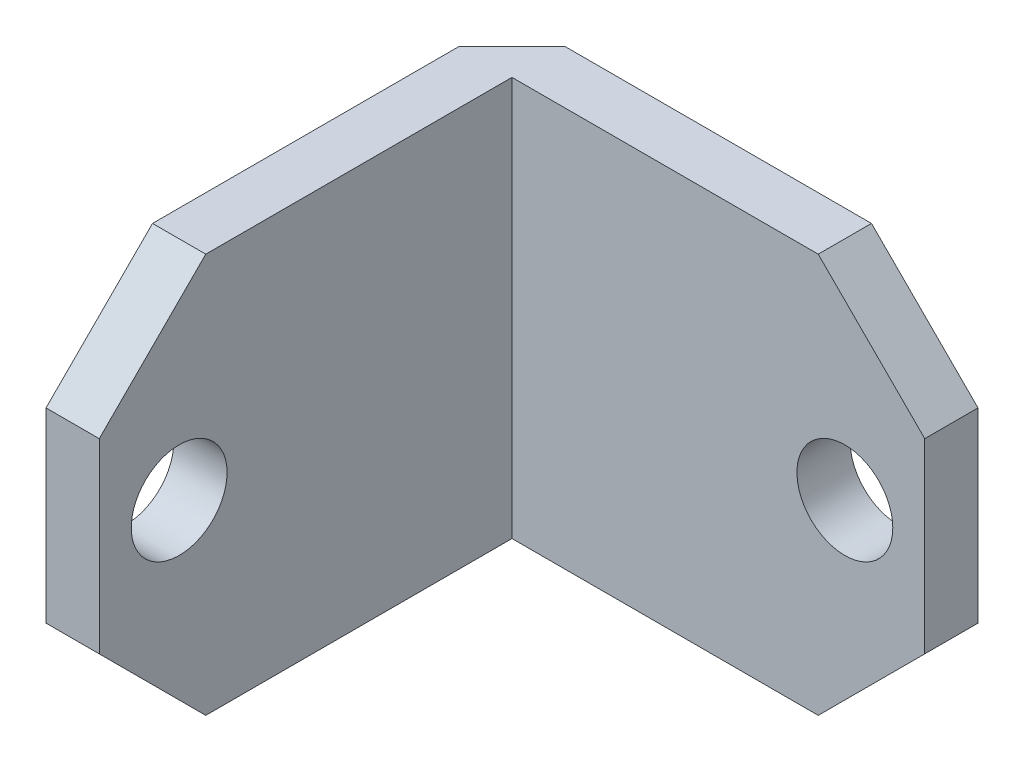
SolidWorks part; units mm, degrees
ref_plane "Front Plane" through (0, 0, 0) normal (0, 0, 1) x (1, 0, 0)
ref_plane "Top Plane" through (0, 0, 0) normal (0, 1, 0) x (1, 0, 0)
ref_plane "Right Plane" through (0, 0, 0) normal (1, 0, 0) x (0, 0, -1)
sketch "Sketch1" plane through (0, 0, 0) normal (0, 1, 0) x (1, 0, 0)
  line L1 (0, 0) -> (2.54, 0)
  line L2 (0, 0) -> (0, 22.225)
  line L4 (2.54, 0) -> (2.54, 19.685)
  line L5 (0, 22.225) -> (22.225, 22.225)
  line L6 (0, 22.225) -> (0, 14.8757)
  line L7 (2.54, 19.685) -> (22.225, 19.685)
  line L8 (22.225, 22.225) -> (22.225, 19.685)
  dimension "D1" = 19.685
  dimension "D3" = 2.54
  dimension "D4" = 2.54
extrude "Boss-Extrude1" add sketch "Sketch1" along normal blind 19.05 contours L8 L5 L2 L1 L4 L7
sketch "Sketch2" plane through (0, 0, -19.685) normal (0, 0, 1) x (1, 0, 0)
  line L0 (2.54, 19.05) -> (2.54, 0) construction
  line L2 (22.225, 19.05) -> (22.225, 0) construction
  circle A0 centre (18.415, 9.525) radius 2.286
  point P7 (22.225, 9.525)
  dimension "D1" = 4.572
  dimension "D2" = 15.875
extrude "Cut-Extrude1" cut sketch "Sketch2" against normal blind 2.54
sketch "Sketch3" plane through (2.54, 0, 0) normal (1, 0, 0) x (0, 0, -1)
  line L1 (19.685, 19.05) -> (19.685, 0) construction
  line L2 (0, 19.05) -> (0, 0) construction
  circle A0 centre (3.81, 9.525) radius 2.286
  point P7 (0, 9.525)
  dimension "D1" = 4.572
  dimension "D3" = 15.875
extrude "Cut-Extrude2" cut sketch "Sketch3" against normal blind 2.54
chamfer "Chamfer1" distance 5.08 angle 45 4 edges at (1.27, 0, 0) (22.225, 0, -20.955) (22.225, 19.05, -20.955) (1.27, 19.05, 0)
chamfer "Chamfer2" distance 2.54 angle 45 1 edges at (0, 9.525, -22.225)
